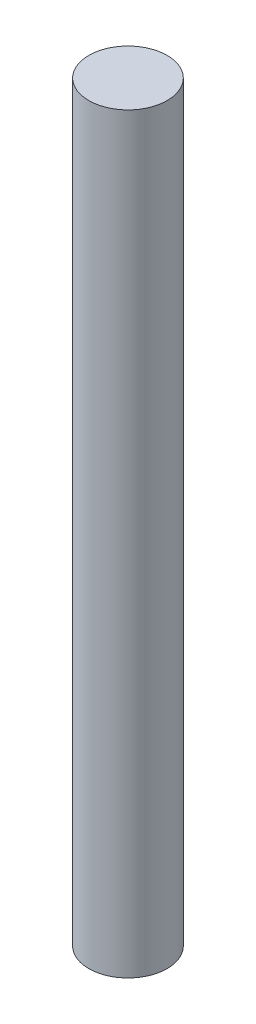
SolidWorks part; units mm, degrees
ref_plane "Alzado" through (0, 0, 0) normal (0, 0, 1) x (1, 0, 0)
ref_plane "Planta" through (0, 0, 0) normal (0, 1, 0) x (1, 0, 0)
ref_plane "Vista lateral" through (0, 0, 0) normal (1, 0, 0) x (0, 0, -1)
sketch "Croquis1" plane through (0, 0, 0) normal (0, 1, 0) x (1, 0, 0)
  circle A0 centre (0, 0) radius 0.5
  dimension "D1" = 1
extrude "Saliente-Extruir1" add sketch "Croquis1" along normal blind 8 and the other way blind 1.6
